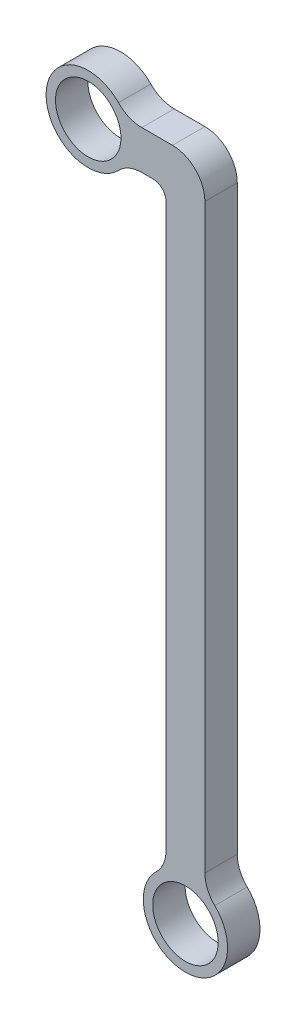
SolidWorks part; units mm, degrees
material "ABS"
ref_plane "Plan de face" through (0, 0, 0) normal (0, 0, 1) x (1, 0, 0)
ref_plane "Plan de dessus" through (0, 0, 0) normal (0, 1, 0) x (1, 0, 0)
ref_plane "Plan de droite" through (0, 0, 0) normal (1, 0, 0) x (0, 0, -1)
sketch "Esquisse1" plane through (154.1307, 0, 0) normal (0, 0, 1) x (1, 0, 0)
  line L0 (-135.0807, 0) -> (-135.0807, -127) construction
  line L1 (-138.8907, -6.35) -> (-138.8907, -116.5081)
  line L2 (-131.2707, -2.54) -> (-131.2707, -116.5081)
  line L3 (-143.6387, 3.81) -> (-137.6207, 3.81)
  line L4 (-141.4307, -3.81) -> (-143.6387, -3.81)
  line L5 (-154.1307, 0) -> (-135.0807, 0) construction
  arc A1 (-140.8233, -121.0698) -> (-129.338, -121.0698) centre (-135.0807, -127) ccw
  circle A2 centre (-135.0807, -127) radius 6.4135
  circle A3 centre (-154.1307, 0) radius 6.4135
  arc A4 (-148.2004, 5.7426) -> (-148.2004, -5.7426) centre (-154.1307, 0) ccw
  arc A6 (-138.8907, -6.35) -> (-141.4307, -3.81) centre (-141.4307, -6.35) ccw
  arc A7 (-131.2707, -2.54) -> (-137.6207, 3.81) centre (-137.6207, -2.54) ccw
  arc A8 (-143.6387, 3.81) -> (-148.2004, 5.7426) centre (-143.6387, 10.16) cw
  arc A9 (-143.6387, -3.81) -> (-148.2004, -5.7426) centre (-143.6387, -10.16) ccw
  arc A10 (-138.8907, -116.5081) -> (-140.8233, -121.0698) centre (-145.2407, -116.5081) cw
  arc A11 (-131.2707, -116.5081) -> (-129.338, -121.0698) centre (-124.9207, -116.5081) ccw
  point P24 (-138.8907, -119.6768)
  point P27 (-131.2707, -119.6768)
  dimension "D1" = 12.827
  dimension "D3" = 2.54
  dimension "D5" = 6.35
  dimension "D6" = 6.35
  dimension "D7" = 6.35
  dimension "D4" = 3.81
  dimension "D8" = 127
  dimension "D9" = 3.81
  dimension "D10" = 3.81
  dimension "D11" = 19.05
extrude "Boss.-Extru.1" add sketch "Esquisse1" along normal blind 6.35
